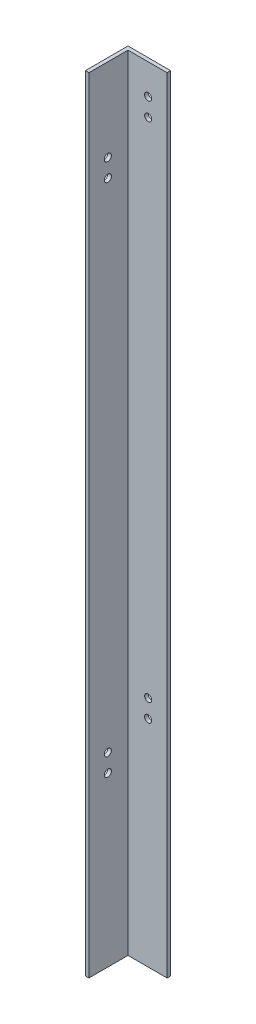
SolidWorks part; units mm, degrees
material "Acero al carbono no aleado"
ref_plane "Alzado" through (0, 0, 0) normal (0, 0, 1) x (1, 0, 0)
ref_plane "Planta" through (0, 0, 0) normal (0, 1, 0) x (1, 0, 0)
ref_plane "Vista lateral" through (0, 0, 0) normal (1, 0, 0) x (0, 0, -1)
sketch "Croquis1" plane through (0, 0, 0) normal (0, 0, 1) x (1, 0, 0)
  line L0 (0, 0) -> (0, 700)
  line L1 (-38.1, 700) -> (0, 700)
  line L2 (-38.1, 700) -> (-38.1, 0)
  line L3 (-38.1, 0) -> (0, 0)
  dimension "D1" = 38.1
  dimension "D2" = 700
extrude "Saliente-Extruir1" add sketch "Croquis1" along normal blind 3.2
sketch "Croquis2" plane through (0, 0, 3.2) normal (0, 0, 1) x (1, 0, 0)
  line L7 (-38.1, 0) -> (0, 0) construction
  line L8 (-38.1, 700) -> (-34.9, 700)
  line L9 (-38.1, 700) -> (-38.1, 0)
  line L10 (-38.1, 0) -> (-34.9, 0)
  line L11 (-34.9, 700) -> (-34.9, 0)
  dimension "D1" = 3.2
extrude "Saliente-Extruir2" add sketch "Croquis2" along normal blind 34.9
sketch "Croquis5" plane through (0, 0, 3.2) normal (0, 0, 1) x (1, 0, 0)
  line L2 (-34.9, 0) -> (-34.9, 700) construction
  line L3 (0, 700) -> (-34.9, 700) construction
  line L4 (-34.9, 0) -> (0, 0) construction
  circle A0 centre (-16.9, 673) radius 3.175
  circle A1 centre (-16.9, 657) radius 3.175
  circle A4 centre (-16.9, 208) radius 3.175
  circle A5 centre (-16.9, 192) radius 3.175
  dimension "D1" = 16
  dimension "D6" = 192
  dimension "D2" = 18
  dimension "D3" = 27
  dimension "D4" = 16
extrude "Cortar-Extruir1" cut sketch "Croquis5" against normal blind 10
sketch "Croquis6" plane through (-34.9, 0, 0) normal (1, 0, 0) x (0, 0, -1)
  line L0 (-3.2, 0) -> (-3.2, 700) construction
  line L2 (-38.1, 700) -> (-3.2, 700) construction
  line L3 (-38.1, 0) -> (-3.2, 0) construction
  circle A0 centre (-21.2, 626) radius 3.175
  circle A1 centre (-21.2, 610) radius 3.175
  circle A4 centre (-21.2, 166) radius 3.175
  circle A5 centre (-21.2, 150) radius 3.175
  dimension "D4" = 16
  dimension "D6" = 150
  dimension "D1" = 16
  dimension "D3" = 74
  dimension "D5" = 18
extrude "Cortar-Extruir2" cut sketch "Croquis6" against normal blind 10
